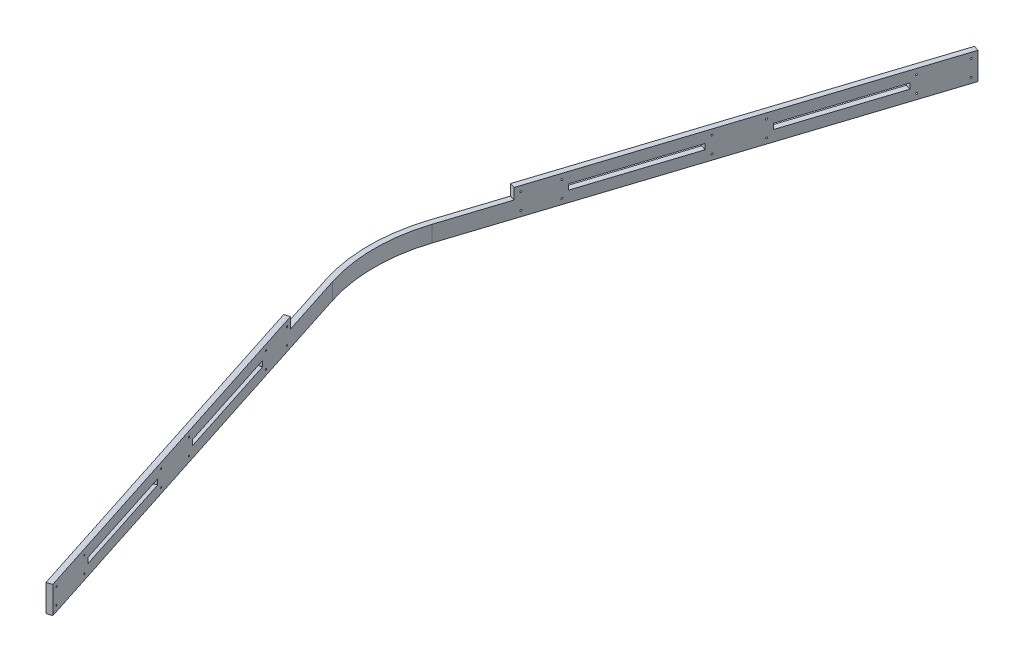
SolidWorks part; units mm, degrees
ref_plane "Front Plane" through (0, 0, 0) normal (0, 0, 1) x (1, 0, 0)
ref_plane "Top Plane" through (0, 0, 0) normal (0, 1, 0) x (1, 0, 0)
ref_plane "Right Plane" through (0, 0, 0) normal (1, 0, 0) x (0, 0, -1)
sketch "Sketch2" plane through (0, 0, 0) normal (0, 1, 0) x (1, 0, 0)
  line L0 (-295.0403, 95.1378) -> (-34.5174, 903.069) construction
  line L1 (-25, 910) -> (25, 910) construction
  line L2 (0, 0) -> (0, 979.251) construction
  line L3 (-181.6808, 251.1814) -> (-9.5174, 785.0928) construction
  line L4 (295.0403, 95.1378) -> (32.2825, 910) construction
  line L5 (181.6808, 251.1814) -> (9.5174, 785.0928) construction
  line L8 (-591.5307, 0) -> (570.3863, 0) construction
  line L9 (181.6808, -251.1814) -> (9.5174, -785.0928) construction
  line L10 (295.0403, -95.1378) -> (32.2825, -910) construction
  line L11 (-181.6808, -251.1814) -> (-9.5174, -785.0928) construction
  line L12 (-25, -910) -> (25, -910) construction
  line L13 (-295.0403, -95.1378) -> (-34.5174, -903.069) construction
  circle A0 centre (0, 0) radius 250 construction
  arc A1 (181.6808, 251.1814) -> (-181.6808, 251.1814) centre (0, 0) ccw construction
  arc A2 (-9.5174, 785.0928) -> (9.5174, 785.0928) centre (0, 782.0238) cw construction
  arc A3 (-295.0403, 95.1378) -> (-295.0403, -95.1378) centre (0, 0) ccw construction
  arc A4 (-25, 910) -> (-34.5174, 903.069) centre (-25, 900) ccw construction
  arc A5 (25, 910) -> (34.5174, 903.069) centre (25, 900) cw construction
  arc A22 (25, -910) -> (34.5174, -903.069) centre (25, -900) ccw construction
  arc A23 (-25, -910) -> (-34.5174, -903.069) centre (-25, -900) cw construction
  arc A24 (-9.5174, -785.0928) -> (9.5174, -785.0928) centre (0, -782.0238) ccw construction
  arc A25 (181.6808, -251.1814) -> (-181.6808, -251.1814) centre (0, 0) cw construction
  arc A26 (-181.6808, -251.1814) -> (181.6808, -251.1814) centre (0, 0) ccw construction
  arc A27 (295.0403, -95.1378) -> (295.0403, 95.1378) centre (0, 0) ccw construction
  point P15 (0, 814.6081)
  point P17 (-32.2825, 910)
  point P21 (0, 910)
  point P69 (0, -910)
  dimension "D1" = 500
  dimension "D2" = 10
  dimension "D3" = 10
  dimension "D8" = 60
  dimension "D9" = 910
  dimension "D11" = 50
sketch "Sketch3" plane through (0, 0, 0) normal (0, 1, 0) x (1, 0, 0)
  line L0 (-49.5235, -856.5322) -> (-40.0061, -853.4632)
  line L1 (-233.6611, -285.4864) -> (-295.0403, -95.1378)
  line L2 (-224.1437, -282.4174) -> (-285.5229, -92.0688)
  line L3 (0, 0) -> (-548.9681, 0) construction
  line L4 (-295.0403, -95.1378) -> (-34.5174, -903.069) construction
  line L5 (-70.6957, -758.2889) -> (-80.2131, -761.3579)
  line L6 (-132.0749, -567.9403) -> (-141.5923, -571.0093)
  line L7 (-162.7645, -472.766) -> (-172.2819, -475.835)
  line L8 (0, 1168.7659) -> (0, -1304.5967) construction
  line L9 (-233.6611, -285.4864) -> (-224.1437, -282.4174)
  line L10 (-295.0403, -95.1378) -> (-285.5229, -92.0688) construction
  line L11 (-591.5307, 0) -> (570.3863, 0) construction
  line L13 (-132.0749, 567.9403) -> (-70.6957, 758.2889) construction
  line L14 (-141.5923, -571.0093) -> (-172.2819, -475.835)
  line L15 (-224.1437, -282.4174) -> (-162.7645, -472.766) construction
  line L16 (-172.2819, -475.835) -> (-233.6611, -285.4864) construction
  line L17 (-80.2131, -761.3579) -> (-141.5923, -571.0093) construction
  line L18 (-132.0749, -567.9403) -> (-70.6957, -758.2889) construction
  line L19 (-162.7645, -472.766) -> (-132.0749, -567.9403)
  line L20 (-80.2131, -761.3579) -> (-49.5235, -856.5322)
  line L21 (-70.6957, -758.2889) -> (-40.0061, -853.4632)
  line L22 (-80.2131, 761.3579) -> (-141.5923, 571.0093) construction
  line L23 (-172.2819, 475.835) -> (-233.6611, 285.4864) construction
  line L24 (-224.1437, 282.4174) -> (-162.7645, 472.766) construction
  line L25 (-295.0403, 95.1378) -> (-285.5229, 92.0688) construction
  line L26 (-70.6957, 758.2889) -> (-40.0061, 853.4632)
  line L27 (-80.2131, 761.3579) -> (-49.5235, 856.5322)
  line L28 (-162.7645, 472.766) -> (-132.0749, 567.9403)
  line L29 (-141.5923, 571.0093) -> (-172.2819, 475.835)
  line L30 (-233.6611, 285.4864) -> (-224.1437, 282.4174)
  line L31 (-162.7645, 472.766) -> (-172.2819, 475.835)
  line L32 (-132.0749, 567.9403) -> (-141.5923, 571.0093)
  line L33 (-70.6957, 758.2889) -> (-80.2131, 761.3579)
  line L34 (-224.1437, 282.4174) -> (-285.5229, 92.0688)
  line L35 (-233.6611, 285.4864) -> (-295.0403, 95.1378)
  line L36 (-49.5235, 856.5322) -> (-40.0061, 853.4632)
  arc A0 (-295.0403, 95.1378) -> (-295.0403, -95.1378) centre (0, 0) ccw
  arc A3 (-285.5229, 92.0688) -> (-285.5229, -92.0688) centre (0, 0) ccw
  dimension "D1" = 10
  dimension "D2" = 800
  dimension "D3" = 100
  dimension "D4" = 200
  dimension "D5" = 100
  dimension "D6" = 200
extrude "Boss-Extrude1" add sketch "Sketch3" along normal mid plane 10
sketch "Sketch4" plane through (0, 5, 0) normal (0, 1, 0) x (1, 0, 0)
  line L0 (-224.1437, -282.4174) -> (-285.5229, -92.0688) construction
  line L1 (-49.5235, -856.5322) -> (-40.0061, -853.4632) construction
  line L2 (-172.2819, -475.835) -> (-141.5923, -571.0093) construction
  line L3 (-591.5307, 0) -> (570.3863, 0) construction
  line L4 (-49.5235, -856.5322) -> (-258.2128, -209.3469)
  line L5 (-40.0061, -853.4632) -> (-248.6954, -206.278)
  line L6 (-49.5235, -856.5322) -> (-40.0061, -853.4632)
  line L9 (-49.5235, 856.5322) -> (-40.0061, 853.4632)
  line L10 (-40.0061, 853.4632) -> (-248.6954, 206.278)
  line L11 (-49.5235, 856.5322) -> (-258.2128, 209.3469)
  line L12 (-258.2128, 209.3469) -> (-248.6954, 206.278)
  line L13 (-224.1437, 282.4174) -> (-233.6611, 285.4864) construction
  line L14 (-258.2128, -209.3469) -> (-248.6954, -206.278)
  line L15 (-233.6611, 285.4864) -> (-295.0403, 95.1378) construction
  line L16 (-285.5229, 92.0688) -> (-224.1437, 282.4174) construction
  arc A0 (-285.5229, -92.0688) -> (-285.5229, 92.0688) centre (0, 0) cw construction
  arc A1 (-295.0403, 95.1378) -> (-295.0403, -95.1378) centre (0, 0) ccw construction
  arc A2 (-295.0403, -95.1378) -> (-295.0403, 95.1378) centre (0, 0) cw construction
  dimension "D1" = 120
extrude "Boss-Extrude2" add sketch "Sketch4" along normal blind 20
sketch "Sketch5" plane through (0, -5, 0) normal (0, -1, 0) x (1, 0, 0)
  line L0 (-49.5235, 856.5322) -> (-40.0061, 853.4632)
  line L1 (-40.0061, 853.4632) -> (-285.5229, 92.0688)
  line L3 (-295.0403, 95.1378) -> (-34.5174, 903.069) construction
  line L4 (-295.0403, 95.1378) -> (-49.5235, 856.5322)
  line L5 (-591.5307, 0) -> (0, 0) construction
  line L6 (-295.0403, -95.1378) -> (-49.5235, -856.5322)
  line L7 (-40.0061, -853.4632) -> (-285.5229, -92.0688)
  line L8 (-49.5235, -856.5322) -> (-40.0061, -853.4632)
  arc A0 (-285.5229, -92.0688) -> (-285.5229, 92.0688) centre (0, 0) cw
  arc A2 (-295.0403, -95.1378) -> (-295.0403, 95.1378) centre (0, 0) cw
extrude "Boss-Extrude3" add sketch "Sketch5" along normal blind 20
sketch "Sketch8" plane through (-295.0403, 0, 95.1378) normal (-0.9517, 0, 0.3069) x (0.3069, 0, 0.9517)
  line L0 (800, 25) -> (800, -25) construction
  line L1 (120, 25) -> (800, 25) construction
  line L2 (834.5529, 0) -> (-174.8818, 0) construction
  line L3 (750, 38.0761) -> (750, -40.0728) construction
  line L4 (600, 5) -> (600, 42.402) construction
  line L5 (500, 5) -> (700, 5) construction
  line L6 (300, 5) -> (300, 59.2683) construction
  line L7 (200, 5) -> (400, 5) construction
  line L8 (120, 25) -> (120, 5) construction
  circle A0 centre (790, 15) radius 1.5
  circle A1 centre (710, 15) radius 1.5
  circle A2 centre (410, 15) radius 1.5
  circle A3 centre (490, 15) radius 1.5
  circle A4 centre (130, 15) radius 1.5
  circle A5 centre (190, 15) radius 1.5
  circle A6 centre (790, -15) radius 1.5
  circle A7 centre (190, -15) radius 1.5
  circle A8 centre (130, -15) radius 1.5
  circle A9 centre (490, -15) radius 1.5
  circle A10 centre (410, -15) radius 1.5
  circle A11 centre (710, -15) radius 1.5
  dimension "D1" = 3
  dimension "D2" = 10
  dimension "D3" = 10
  dimension "D4" = 50
  dimension "D5" = 10
extrude "Cut-Extrude2" cut sketch "Sketch8" against normal through all
mirror "Mirror1" about plane through (0, 0, 0) normal (0, 0, 1) of "Cut-Extrude2"
